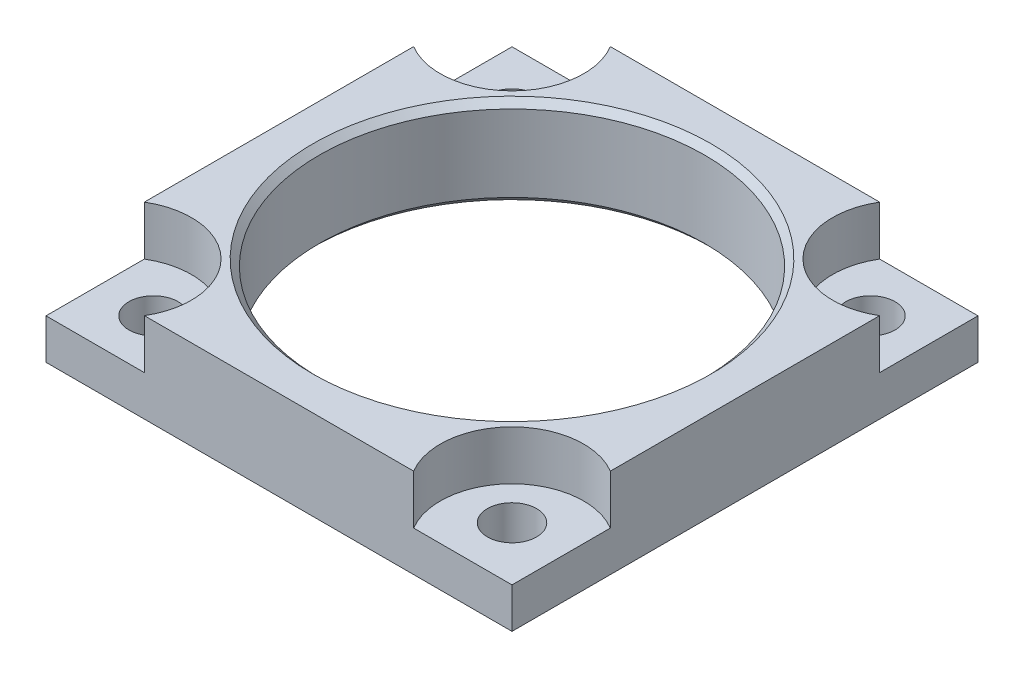
SolidWorks part; units mm, degrees
material "Alloy Steel"
ref_plane "Front Plane" through (0, 0, 0) normal (0, 0, 1) x (1, 0, 0)
ref_plane "Top Plane" through (0, 0, 0) normal (0, 1, 0) x (1, 0, 0)
ref_plane "Right Plane" through (0, 0, 0) normal (1, 0, 0) x (0, 0, -1)
sketch "Sketch1" plane through (0, 0, 0) normal (0, 1, 0) x (1, 0, 0)
  line L0 (41.275, 41.275) -> (-41.275, -41.275) construction
  line L1 (-41.275, 41.275) -> (41.275, 41.275)
  line L2 (-41.275, 41.275) -> (-41.275, -41.275)
  line L3 (-41.275, -41.275) -> (41.275, -41.275)
  line L4 (41.275, 41.275) -> (41.275, -41.275)
  line L5 (-41.275, 41.275) -> (41.275, -41.275) construction
  circle A0 centre (0, 0) radius 34.1503
  dimension "D3" = 68.3006
  dimension "D1" = 82.55
  dimension "D2" = 82.55
extrude "Extrude1" add sketch "Sketch1" along normal blind 15.875
sketch "Sketch2" plane through (0, 15.875, 0) normal (0, 1, 0) x (1, 0, 0)
  line L0 (-41.275, -41.275) -> (41.275, -41.275) construction
  line L1 (41.275, -41.275) -> (41.275, 41.275) construction
  line L2 (23.8533, -41.275) -> (41.275, -41.275)
  line L3 (41.275, -41.275) -> (41.275, -23.8533)
  line L4 (0, 0) -> (-25.3528, 0) construction
  line L5 (0, 0) -> (0, 27.5861) construction
  line L6 (41.275, 41.275) -> (41.275, 23.8533)
  line L7 (23.8533, 41.275) -> (41.275, 41.275)
  line L8 (-23.8533, 41.275) -> (-41.275, 41.275)
  line L9 (-41.275, 41.275) -> (-41.275, 23.8533)
  line L10 (-41.275, -41.275) -> (-41.275, -23.8533)
  line L11 (-23.8533, -41.275) -> (-41.275, -41.275)
  arc A0 (41.275, -23.8533) -> (23.8533, -41.275) centre (34.7472, -34.7472) ccw
  arc A1 (41.275, 23.8533) -> (23.8533, 41.275) centre (34.7472, 34.7472) cw
  arc A2 (-41.275, 23.8533) -> (-23.8533, 41.275) centre (-34.7472, 34.7472) ccw
  arc A3 (-41.275, -23.8533) -> (-23.8533, -41.275) centre (-34.7472, -34.7472) cw
  dimension "D1" = 12.7
  dimension "D2" = 34.7472
  dimension "D3" = 34.7472
extrude "Cut-Extrude1" cut sketch "Sketch2" against normal blind 8.7376
hole_wizard "Hole1" positions "Sketch4" profile "Sketch3" legacy end condition up to next
sketch "Sketch4" plane through (0, 7.1374, 0) normal (0, 1, 0) x (-1, 0, 0)
  point P0 (31.75, 31.75)
  point P6 (31.75, -31.75)
  point P9 (-31.75, 31.75)
  point P11 (-31.75, -31.75)
  dimension "D1" = 31.75
  dimension "D2" = 31.75
  dimension "D3" = 63.5
  dimension "D4" = 63.5
sketch "Sketch3" plane through (-31.75, 7.1374, 31.75) normal (1, 0, 0) x (0, 0, 1)
  line L0 (0, 0) -> (0, 7.1374)
  line L1 (0, 7.1374) -> (4.3561, 7.1374)
  line L2 (4.3561, 7.1374) -> (4.3561, 0)
  line L3 (4.3561, 0) -> (0, 0)
  line L4 (0, 110) -> (0, -10) construction
  dimension "Diameter" = 8.7122
  dimension "Depth" = 7.1374
sketch "Sketch5" plane through (0, 0, 0) normal (1, 0, 0) x (0, 0, -1)
  line L0 (0, 0) -> (0, 13.7269) construction
  line L1 (-22.3145, 7.9375) -> (-9.8575, 7.9375) construction
  line L2 (-22.0472, 15.875) -> (-41.275, 15.875) construction
  line L3 (-41.275, 0) -> (41.275, 0) construction
  line L4 (-35.306, 15.875) -> (-34.1503, 15.875)
  line L5 (-34.1503, 15.875) -> (-34.1503, 14.7193)
  line L6 (-34.1503, 15.875) -> (-34.1503, 0) construction
  line L7 (-34.1503, 14.7193) -> (-35.306, 15.875)
  line L8 (-34.1503, 1.1557) -> (-35.306, 0)
  line L9 (-34.1503, 0) -> (-34.1503, 1.1557)
  line L10 (-35.306, 0) -> (-34.1503, 0)
  dimension "D1" = 45
  dimension "D2" = 70.612
revolve "Cut-Revolve1" cut sketch "Sketch5" angle 360 about L0
